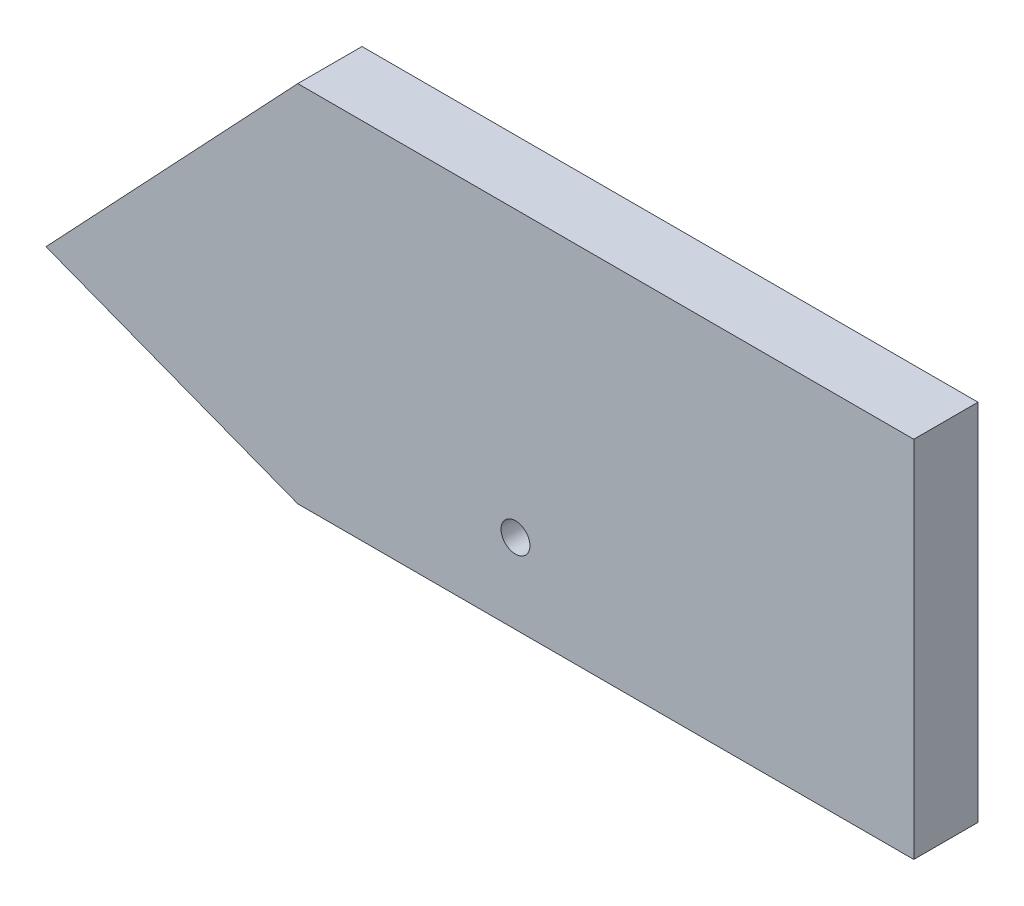
SolidWorks part; units mm, degrees
ref_plane "XY" through (0, 0, 0) normal (0, 0, 1) x (1, 0, 0)
ref_plane "XZ" through (0, 0, 0) normal (0, 1, 0) x (1, 0, 0)
ref_plane "YZ" through (0, 0, 0) normal (1, 0, 0) x (0, 0, -1)
sketch "ref externes" plane through (0, 0, 129.9356) normal (0, 0, 1) x (1, 0, 0)
  line L0 (-556.8868, -138.2683) -> (-596.0822, -179.8523)
  line L1 (-596.0822, -179.8523) -> (-556.8868, -194.929)
  line L4 (-460.9794, -138.2683) -> (-556.8868, -138.2683)
  line L5 (-556.8868, -138.2683) -> (-556.8868, -194.929)
  line L6 (-556.8868, -194.929) -> (-460.9794, -194.929)
  line L7 (-460.9794, -194.929) -> (-460.9794, -138.2683)
  line L8 (-460.9794, -138.2683) -> (-556.8868, -138.2683)
  line L10 (-556.8868, -194.929) -> (-460.9794, -194.929)
  line L11 (-460.9794, -194.929) -> (-460.9794, -138.2683)
  point P7 (-557.5747, -194.6644)
  dimension "D2" = 39.1954
  dimension "D3" = 15.0767
  dimension "D1" = 0
sketch "ref externes (internes)" plane through (0, 0, 0) normal (0, 0, 1) x (1, 0, 0)
  line L0 (-556.8868, -138.2683) -> (-556.8868, -194.929) construction
  line L8 (-460.9794, -138.2683) -> (-556.8868, -138.2683)
  line L10 (-556.8868, -194.929) -> (-460.9794, -194.929)
  line L11 (-460.9794, -194.929) -> (-460.9794, -138.2683)
  line L20 (-460.9794, -138.2683) -> (-556.8868, -138.2683)
  line L22 (-556.8868, -194.929) -> (-460.9794, -194.929)
  line L23 (-460.9794, -194.929) -> (-460.9794, -138.2683)
  line L25 (-556.8868, -138.2683) -> (-596.0822, -179.8523)
  line L26 (-556.8868, -138.2683) -> (-596.0822, -179.8523)
  line L27 (-596.0822, -179.8523) -> (-556.8868, -194.929)
  line L28 (-596.0822, -179.8523) -> (-556.8868, -194.929)
  dimension "D1" = 0
extrude "Boss.-Extru.1" add sketch "ref externes (internes)" along normal blind 10
hole_wizard "Dégagement M41" positions "Esquisse12" profile "Esquisse13" hole size "M4" standard "ISO" end condition through all
sketch "Esquisse12" plane through (0, 0, 10) normal (0, 0, 1) x (1, 0, 0)
  line L0 (-563.851, -154.5749) -> (-522.988, -182.5109) construction
  line L1 (-522.988, -182.5109) -> (-522.988, -154.5749) construction
  line L2 (-563.851, -154.5749) -> (-467.9436, -154.5749) construction
  line L3 (-522.988, -154.5749) -> (-563.851, -154.5749) construction
  point P0 (-522.988, -182.5109)
  dimension "D1" = 34.359
  dimension "D2" = 49.4995
sketch "Esquisse13" plane through (-522.988, -182.5109, 10) normal (1, 0, 0) x (0, -1, 0)
  line L0 (0, 0) -> (0, 10)
  line L1 (0, 10) -> (2.25, 10)
  line L2 (2.25, 10) -> (2.25, 0)
  line L5 (2.25, 0) -> (0, 0)
  line L11 (0, -6.35) -> (0, 107.95) construction
  dimension "Diamètre du perçage jusqu'au prochain" = 4.5
  dimension "Profondeur du perçage jusqu'au prochain" = 10
